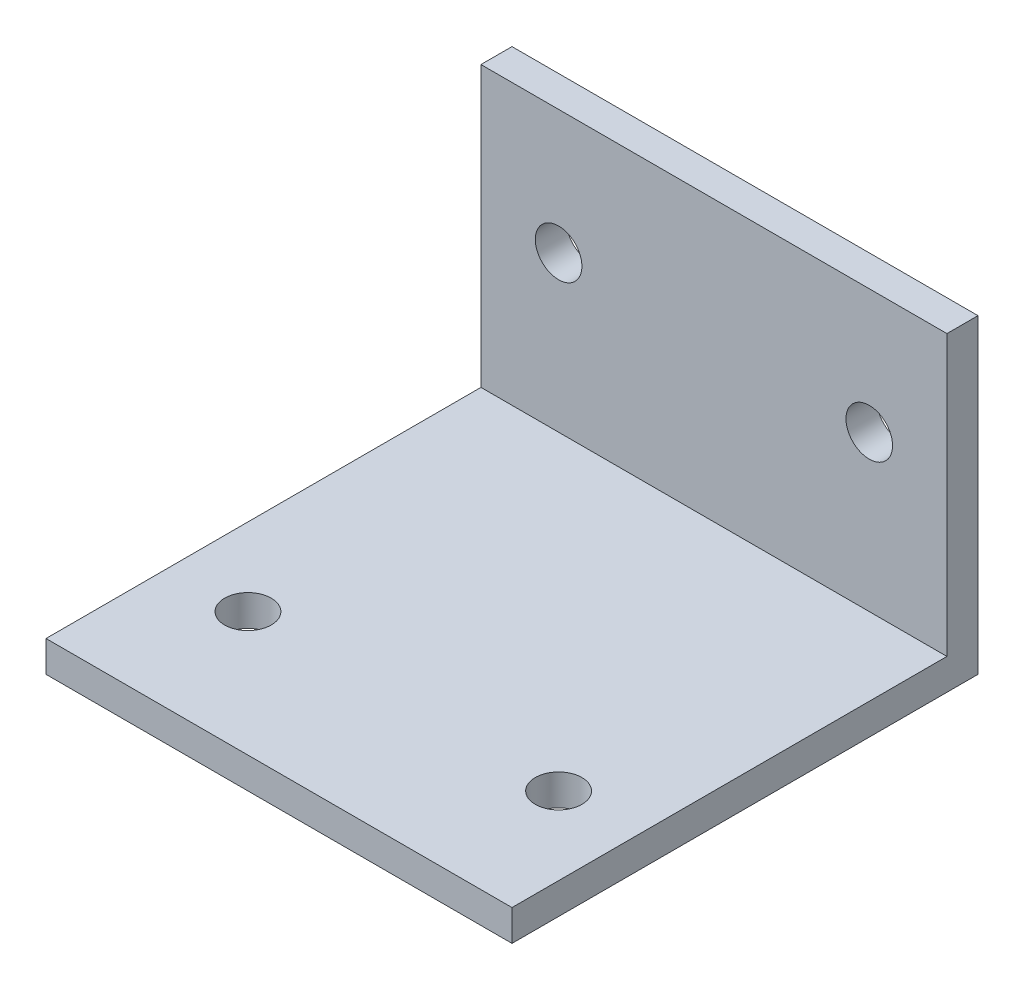
SolidWorks part; units mm, degrees
ref_plane "前视基准面" through (0, 0, 0) normal (0, 0, 1) x (1, 0, 0)
ref_plane "上视基准面" through (0, 0, 0) normal (0, 1, 0) x (1, 0, 0)
ref_plane "右视基准面" through (0, 0, 0) normal (1, 0, 0) x (0, 0, -1)
sketch "草图1" plane through (0, 0, 0) normal (0, 0, 1) x (1, 0, 0)
  line L1 (-15, 19) -> (15, 19)
  line L2 (-15, 19) -> (-15, -19)
  line L3 (-15, -19) -> (15, -19)
  line L4 (15, 19) -> (15, -19)
  line L5 (-15, 19) -> (15, -19) construction
  line L6 (-15, -19) -> (15, 19) construction
  point P0 (0, 0)
  dimension "D1" = 30
  dimension "D2" = 38
extrude "凸台-拉伸1" add sketch "草图1" along normal blind 3
sketch "草图2" plane through (0, 0, 3) normal (0, 0, 1) x (1, 0, 0)
  line L0 (15, -19) -> (15, 19) construction
  line L1 (-15, -19) -> (15, -19)
  line L2 (-15, -19) -> (-15, -16)
  line L3 (-15, -16) -> (15, -16)
  line L4 (15, -19) -> (15, -16)
  dimension "D1" = 3
extrude "凸台-拉伸2" add sketch "草图2" along normal blind 35
sketch "草图3" plane through (0, 0, 3) normal (0, 0, 1) x (1, 0, 0)
  line L0 (15, -16) -> (15, 19) construction
  line L1 (-15, 19) -> (-15, -16) construction
  line L2 (15, 19) -> (-15, 19) construction
  circle A0 centre (-10, -6) radius 1.5
  circle A1 centre (10, -6) radius 1.5
  dimension "D1" = 3
  dimension "D2" = 3
  dimension "D3" = 5
  dimension "D4" = 5
  dimension "D5" = 25
  dimension "D6" = 25
extrude "切除-拉伸1" cut sketch "草图3" against normal blind 35
sketch "草图4" plane through (0, -16, 0) normal (0, 1, 0) x (1, 0, 0)
  line L1 (15, -38) -> (15, -3) construction
  line L2 (-15, -38) -> (-15, -3) construction
  line L3 (15, -38) -> (-15, -38) construction
  circle A0 centre (-10, -23) radius 1.5
  circle A1 centre (10, -23) radius 1.5
  dimension "D1" = 3
  dimension "D2" = 3
  dimension "D3" = 5
  dimension "D4" = 5
  dimension "D5" = 15
extrude "切除-拉伸2" cut sketch "草图4" against normal blind 35
sketch "草图5" plane through (0, -19, 0) normal (0, -1, 0) x (1, 0, 0)
  line L1 (-41.1883, 49.4744) -> (47.4485, 49.4744)
  line L2 (-41.1883, 49.4744) -> (-41.1883, -14.1195)
  line L3 (-41.1883, -14.1195) -> (47.4485, -14.1195)
  line L4 (47.4485, 49.4744) -> (47.4485, -14.1195)
extrude "切除-拉伸3" cut sketch "草图5" against normal blind 1
sketch "草图6" plane through (0, 0, 0) normal (0, 0, -1) x (-1, 0, 0)
  line L1 (25.7068, 22.7168) -> (-23.1859, 22.7168)
  line L2 (25.7068, 22.7168) -> (25.7068, -20.2152)
  line L3 (25.7068, -20.2152) -> (-23.1859, -20.2152)
  line L4 (-23.1859, 22.7168) -> (-23.1859, -20.2152)
  point P4 (-23.1859, -20.2152)
extrude "切除-拉伸4" cut sketch "草图6" against normal blind 1
sketch "草图7" plane through (0, 0, 38) normal (0, 0, 1) x (1, 0, 0)
  line L1 (-19.0979, -12.7811) -> (17.213, -12.7811)
  line L2 (-19.0979, -12.7811) -> (-19.0979, -19.5205)
  line L3 (-19.0979, -19.5205) -> (17.213, -19.5205)
  line L4 (17.213, -12.7811) -> (17.213, -19.5205)
  point P4 (-19.0979, -19.5205)
extrude "切除-拉伸5" cut sketch "草图7" against normal blind 7
sketch "草图8" plane through (0, 19, 0) normal (0, 1, 0) x (1, 0, 0)
  line L1 (19.2375, -7.3482) -> (-19.4018, -7.3482)
  line L2 (19.2375, -7.3482) -> (19.2375, 5.6096)
  line L3 (19.2375, 5.6096) -> (-19.4018, 5.6096)
  line L4 (-19.4018, -7.3482) -> (-19.4018, 5.6096)
extrude "切除-拉伸6" cut sketch "草图8" against normal blind 17
